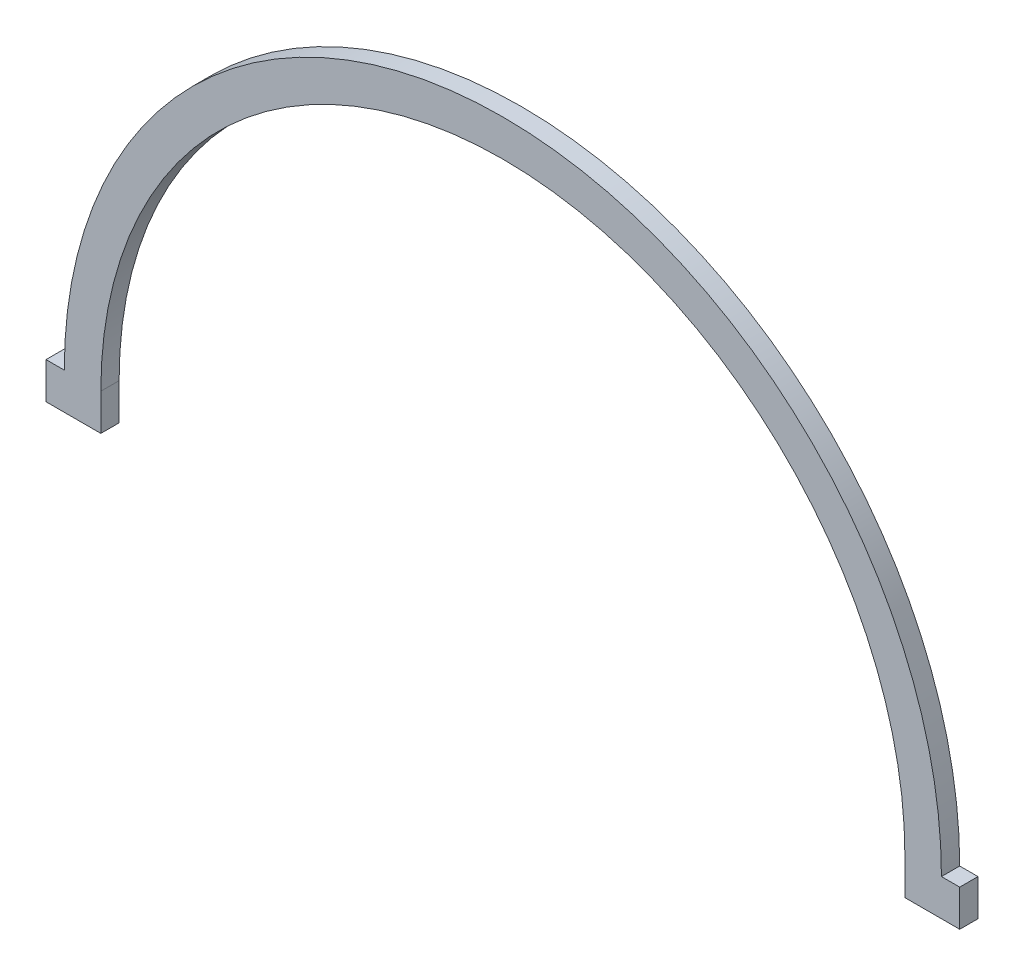
SolidWorks part; units mm, degrees
ref_plane "Front" through (0, 0, 0) normal (0, 0, 1) x (1, 0, 0)
ref_plane "Top" through (0, 0, 0) normal (0, 1, 0) x (1, 0, 0)
ref_plane "Right" through (0, 0, 0) normal (1, 0, 0) x (0, 0, -1)
sketch "Sketch1" plane through (0, 0, 0) normal (0, 0, 1) x (1, 0, 0)
  line L1 (-69.85, 0) -> (69.85, 0)
  line L2 (76.2, 0) -> (79.375, 0)
  line L5 (-79.375, 0) -> (-76.2, 0)
  line L6 (-79.375, 0) -> (-79.375, -6.35)
  line L7 (-79.375, -6.35) -> (79.375, -6.35)
  line L8 (79.375, 0) -> (79.375, -6.35)
  arc A1 (69.85, 0) -> (-69.85, 0) centre (0, 0) ccw
  arc A3 (76.2, 0) -> (-76.2, 0) centre (0, 0) ccw
  dimension "D4" = 6.35
  dimension "D1" = 3.175
  dimension "D2" = 3.175
  dimension "D3" = 158.75
  dimension "D5" = 6.35
extrude "Boss-Extrude1" add sketch "Sketch1" along normal blind 3.175
sketch "Sketch2" plane through (0, 0, 3.175) normal (0, 0, 1) x (1, 0, 0)
  line L0 (-79.375, -6.35) -> (79.375, -6.35) construction
  line L1 (-69.85, 0) -> (69.8324, 0)
  line L2 (-69.85, 0) -> (-69.85, -6.35)
  line L3 (-69.85, -6.35) -> (69.8324, -6.35)
  line L4 (69.8324, 0) -> (69.8324, -6.35)
extrude "Cut-Extrude1" cut sketch "Sketch2" against normal through all
